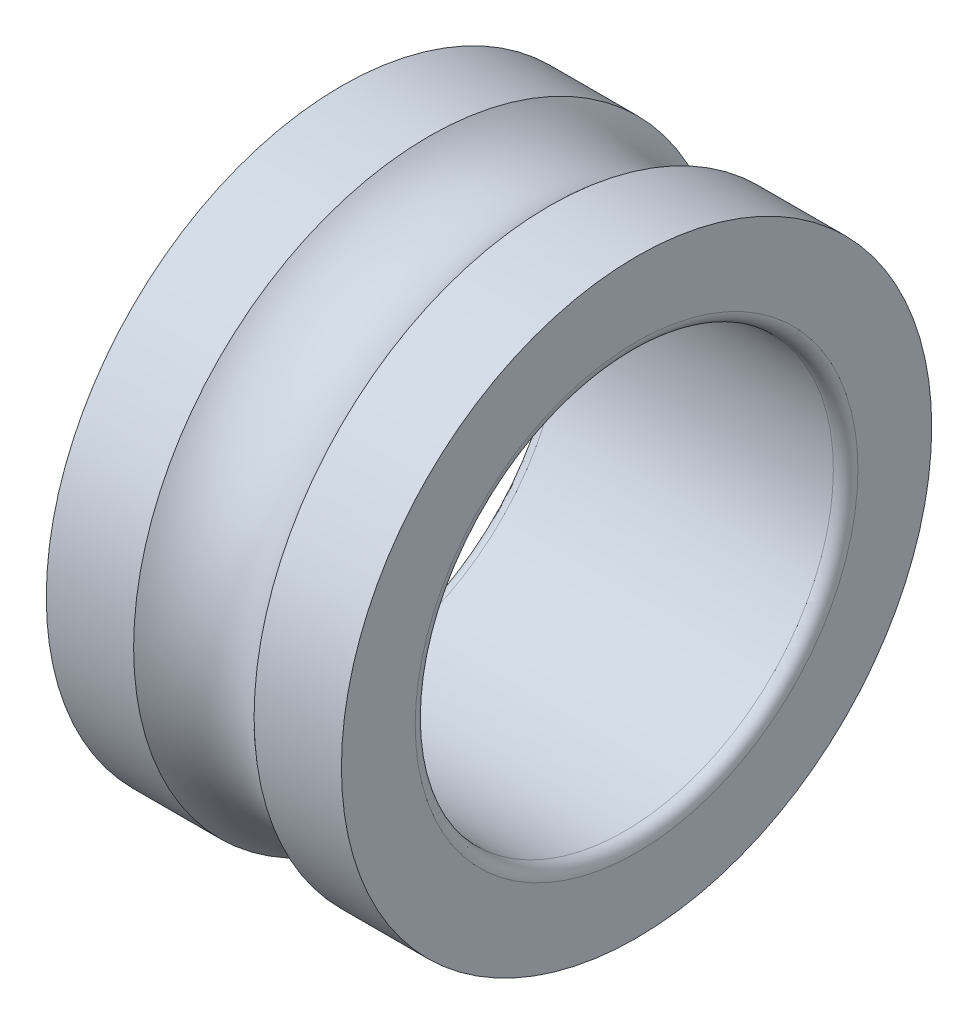
SolidWorks part; units mm, degrees
ref_plane "Front Plane" through (0, 0, 0) normal (0, 0, 1) x (1, 0, 0)
ref_plane "Top Plane" through (0, 0, 0) normal (0, 1, 0) x (1, 0, 0)
ref_plane "Right Plane" through (0, 0, 0) normal (1, 0, 0) x (0, 0, -1)
sketch "Sketch1" plane through (0, 0, 0) normal (0, 0, 1) x (1, 0, 0)
  line L0 (-52.6597, 0) -> (52.6597, 0) construction
  line L1 (-0.7407, 8.5) -> (10.2593, 8.5)
  line L2 (10.7593, 9) -> (10.7593, 12)
  line L3 (10.7593, 12) -> (7.2088, 12)
  line L4 (-1.2407, 12) -> (-1.2407, 9)
  line L7 (2.3098, 12) -> (-1.2407, 12)
  arc A1 (2.3098, 12) -> (7.2088, 12) centre (4.7593, 14.5) ccw
  arc A2 (10.2593, 8.5) -> (10.7593, 9) centre (10.2593, 9) ccw
  arc A3 (-0.7407, 8.5) -> (-1.2407, 9) centre (-0.7407, 9) cw
  point P4 (0, 0)
  point P14 (4.7593, 18.9214)
  dimension "D1" = 8.5
  dimension "D4" = 7
  dimension "D5" = 0.5
  dimension "D2" = 12
  dimension "D6" = 12
revolve "Revolve1" add sketch "Sketch1" angle 360 about L0
